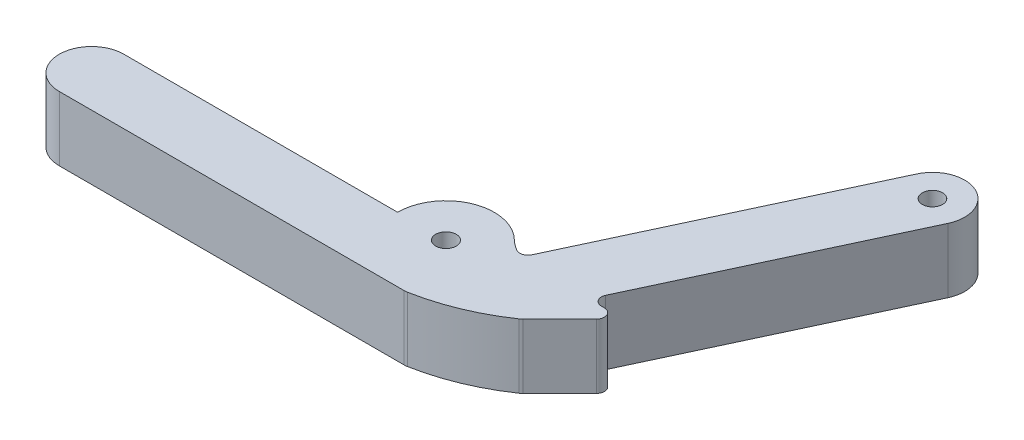
SolidWorks part; units mm, degrees
ref_plane "Front Plane" through (0, 0, 0) normal (0, 0, 1) x (1, 0, 0)
ref_plane "Top Plane" through (0, 0, 0) normal (0, 1, 0) x (1, 0, 0)
ref_plane "Right Plane" through (0, 0, 0) normal (1, 0, 0) x (0, 0, -1)
sketch "Sketch1" plane through (0, 0, 0) normal (0, 1, 0) x (1, 0, 0)
  line L1 (125.9153, 133.8338) -> (-45189.4741, 21264.7469) construction
  line L2 (147.3843, 179.8743) -> (-45168.0051, 21310.7874) construction
  line L3 (35.0956, 75.1509) -> (-72.8411, 75.1509)
  line L5 (-72.8411, 49.6961) -> (38.2706, 49.6961)
  line L6 (110.7461, 77.8565) -> (96.3229, 63.4334)
  line L7 (38.2706, 49.6961) -> (63.1581, 49.6961)
  line L12 (107.3238, 83.2766) -> (108.501, 83.2766)
  line L18 (124.3641, 190.6088) -> (76.0902, 87.085)
  line L19 (147.3843, 179.8743) -> (104.4463, 87.7934)
  arc A1 (64.3217, 49.8036) -> (95.4241, 62.6866) centre (49.4142, 129.7789) ccw
  arc A2 (67.5249, 88.7435) -> (35.0956, 75.1509) centre (54.1589, 75.1509) ccw
  arc A3 (67.5249, 88.7435) -> (71.6788, 85.6469) centre (80.8816, 102.3266) ccw
  circle A4 centre (54.1589, 75.1509) radius 4.05
  arc A5 (64.3217, 49.8036) -> (63.1581, 49.6961) centre (63.1581, 56.0461) cw
  arc A6 (95.4241, 62.6866) -> (96.3229, 63.4334) centre (91.8328, 67.9235) ccw
  arc A8 (108.501, 83.2766) -> (110.7461, 77.8565) centre (108.501, 80.1016) cw
  arc A9 (107.3238, 83.2766) -> (104.4463, 87.7934) centre (107.3238, 86.4516) cw
  arc A10 (71.6788, 85.6469) -> (76.0902, 87.085) centre (73.2126, 88.4269) ccw
  arc A11 (147.3843, 179.8743) -> (124.3641, 190.6088) centre (135.8742, 185.2415) ccw
  circle A12 centre (135.8742, 185.2415) radius 4
  arc A13 (-72.8411, 75.1509) -> (-72.8411, 49.6961) centre (-72.8411, 62.4235) ccw
  point P2 (125.9153, 133.8338)
  dimension "D1" = 19.05
  dimension "D5" = 8.1
  dimension "D6" = 6.35
  dimension "D10" = 3.175
  dimension "D12" = 8
  dimension "D2" = 50.8
  dimension "D3" = 25.4548
  dimension "D4" = 38.1
extrude "Boss-Extrude1" add sketch "Sketch1" along normal blind 25.4
